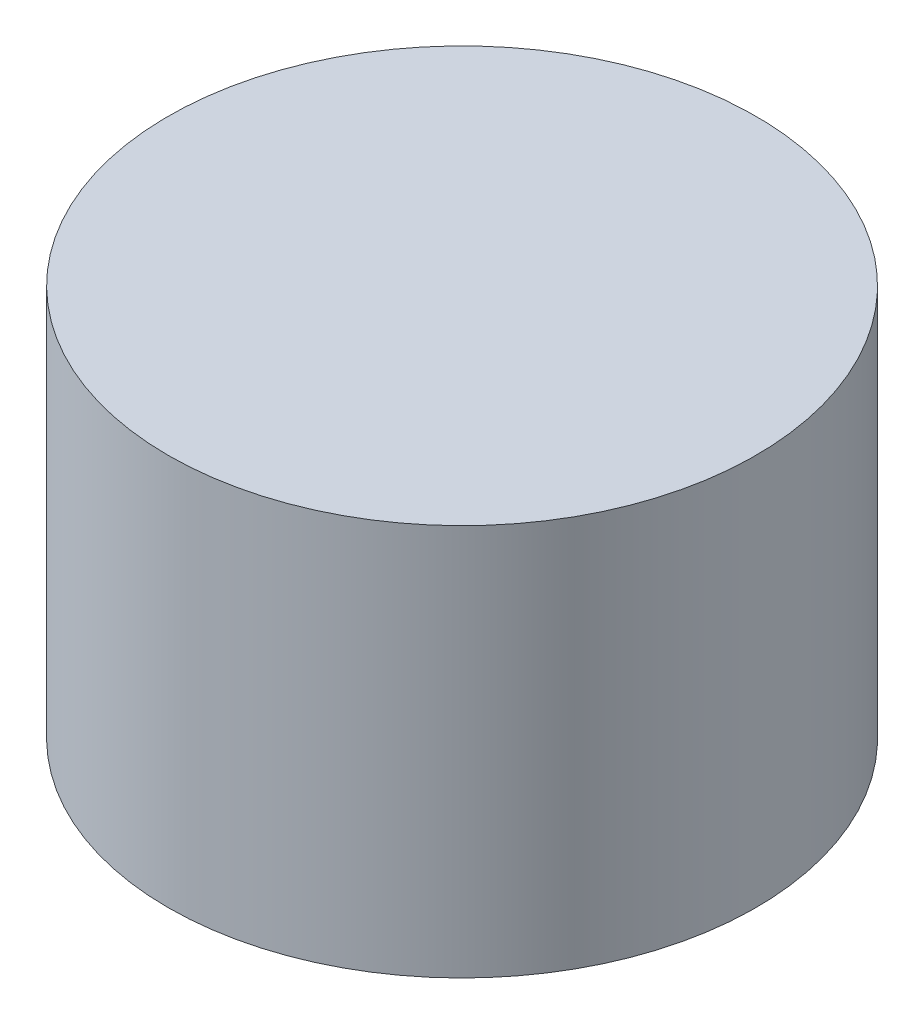
SolidWorks part; units mm, degrees
ref_plane "Front Plane" through (0, 0, 0) normal (0, 0, 1) x (1, 0, 0)
ref_plane "Top Plane" through (0, 0, 0) normal (0, 1, 0) x (1, 0, 0)
ref_plane "Right Plane" through (0, 0, 0) normal (1, 0, 0) x (0, 0, -1)
sketch "Sketch1" plane through (0, 0, 0) normal (0, 1, 0) x (1, 0, 0)
  circle A0 centre (0, 0) radius 1.5
  dimension "3" = 3
extrude "Boss-Extrude1" add sketch "Sketch1" along normal blind 2
